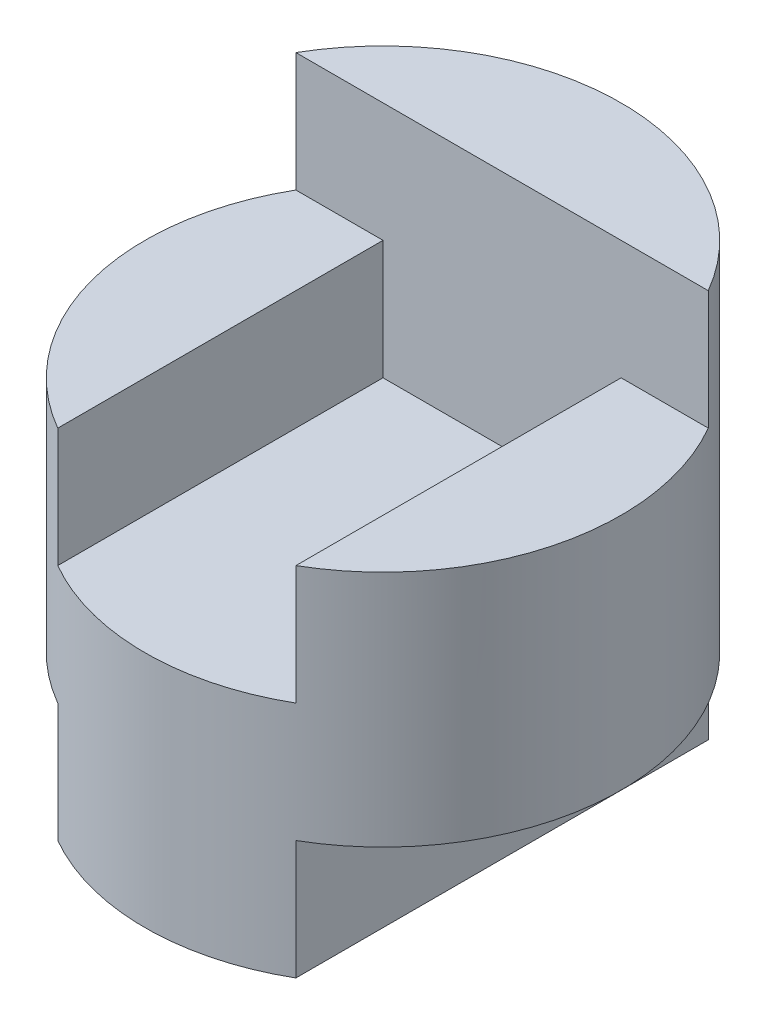
SolidWorks part; units mm, degrees
ref_plane "Front" through (0, 0, 0) normal (0, 0, 1) x (1, 0, 0)
ref_plane "Top" through (0, 0, 0) normal (0, 1, 0) x (1, 0, 0)
ref_plane "Right" through (0, 0, 0) normal (1, 0, 0) x (0, 0, -1)
sketch "Sketch1" plane through (0, 0, 0) normal (0, 1, 0) x (1, 0, 0)
  circle A0 centre (0, 0) radius 2
  dimension "D1" = 4
extrude "Boss-Extrude1" add sketch "Sketch1" along normal blind 4
sketch "Sketch2" plane through (0, 0, 0) normal (0, 0, 1) x (1, 0, 0)
  line L1 (-2, 0) -> (-1, 0)
  line L2 (-2, 0) -> (-2, 1)
  line L3 (-2, 1) -> (-1, 1)
  line L4 (-1, 0) -> (-1, 1)
  line L13 (2, 0) -> (1, 0)
  line L14 (2, 0) -> (2, 1)
  line L15 (2, 1) -> (1, 1)
  line L16 (1, 0) -> (1, 1)
  dimension "D1" = 1
  dimension "D2" = 1
  dimension "D3" = 1
  dimension "D4" = 1
extrude "Cut-Extrude1" cut sketch "Sketch2" against normal mid plane 4
sketch "Sketch3" plane through (0, 0, 0) normal (0, 0, 1) x (1, 0, 0)
  line L0 (-2, 4) -> (2, 4)
  line L1 (2, 4) -> (2, 3)
  line L2 (2, 1) -> (2, 4) construction
  line L3 (2, 3) -> (1, 3)
  line L4 (1, 3) -> (1, 2)
  line L5 (1, 2) -> (-1, 2)
  line L6 (-1, 2) -> (-1, 3)
  line L7 (-1, 3) -> (-2, 3)
  line L8 (-2, 4) -> (-2, 1) construction
  line L9 (-2, 3) -> (-2, 4)
  dimension "D1" = 1
  dimension "D2" = 1
  dimension "D3" = 1
  dimension "D4" = 1
extrude "Cut-Extrude2" cut sketch "Sketch3" against normal blind 1 and the other way blind 4
